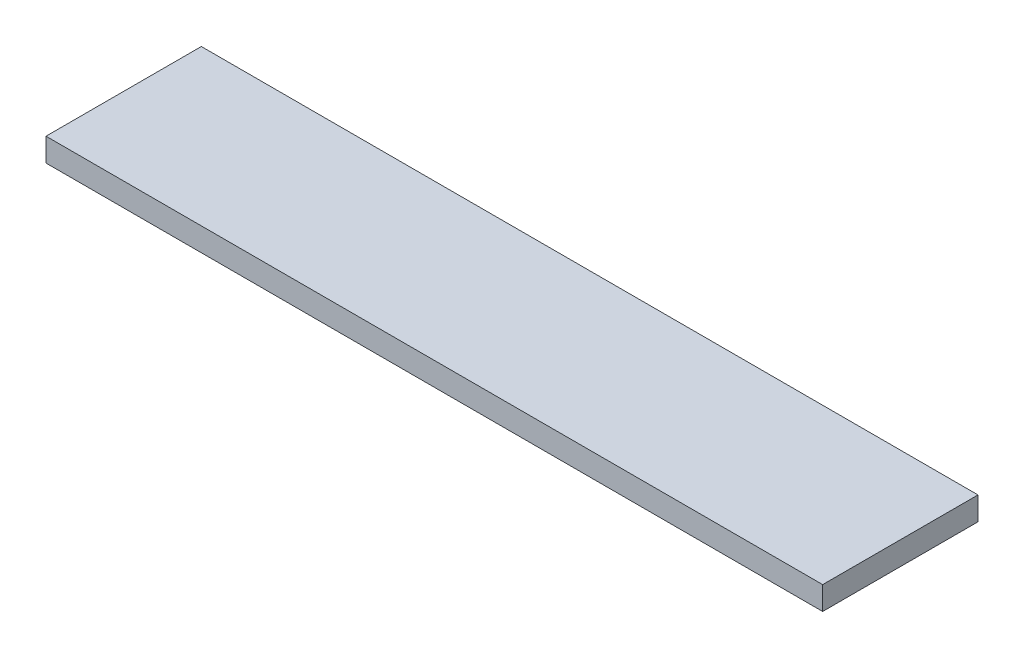
SolidWorks part; units mm, degrees
ref_plane "Спереди" through (0, 0, 0) normal (0, 0, 1) x (1, 0, 0)
ref_plane "Сверху" through (0, 0, 0) normal (0, 1, 0) x (1, 0, 0)
ref_plane "Справа" through (0, 0, 0) normal (1, 0, 0) x (0, 0, -1)
sketch "Эскиз1" plane through (0, 0, 0) normal (1, 0, 0) x (0, 0, -1)
  line L1 (0, 0) -> (20, 0)
  line L2 (0, 0) -> (0, 3)
  line L3 (0, 3) -> (20, 3)
  line L4 (20, 0) -> (20, 3)
extrude "Бобышка-Вытянуть1" add sketch "Эскиз1" along normal blind 100
